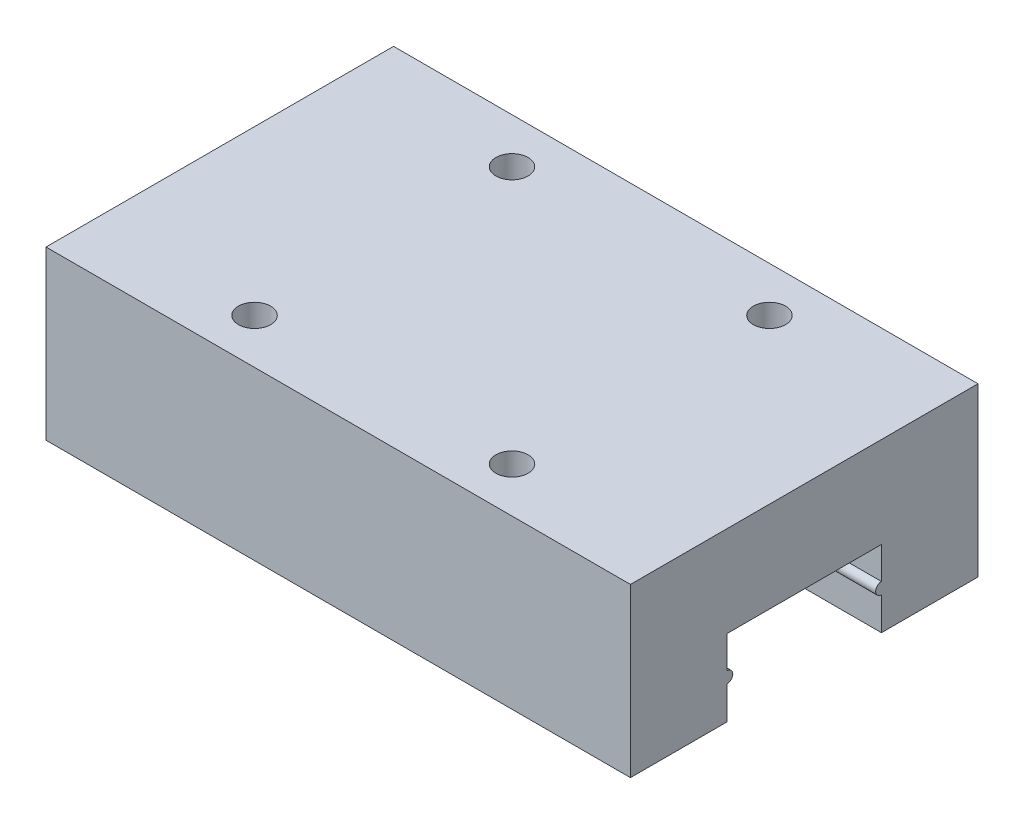
SolidWorks part; units mm, degrees
ref_plane "Front Plane" through (0, 0, 0) normal (0, 0, 1) x (1, 0, 0)
ref_plane "Top Plane" through (0, 0, 0) normal (0, 1, 0) x (1, 0, 0)
ref_plane "Right Plane" through (0, 0, 0) normal (1, 0, 0) x (0, 0, -1)
sketch "Sketch1" plane through (0, 0, 0) normal (1, 0, 0) x (0, 0, -1)
  line L0 (7.5, 0) -> (7.5, 5.9415)
  line L5 (7.5, 0) -> (19.5, 0)
  line L6 (0, 0) -> (0, 13)
  line L7 (0, 13) -> (27, 13)
  line L8 (27, 0) -> (27, 13)
  line L13 (7.5, 5.9415) -> (19.5, 5.9415)
  line L14 (19.5, 5.9415) -> (19.5, 0)
  line L15 (0, 0) -> (7.5, 0)
  line L16 (19.5, 0) -> (27, 0)
  line L17 (13.5, 5.9415) -> (13.5, 0) construction
  arc A0 (7.5, 3.45) -> (7.5, 2.55) centre (7.5, 3) cw
  arc A1 (19.5, 3.45) -> (19.5, 2.55) centre (19.5, 3) ccw
  point P4 (13.5, 0)
  point P12 (7.5, 3)
  dimension "D6" = 0.45
  dimension "D1" = 13
  dimension "D2" = 27
  dimension "D3" = 7.0585
  dimension "D4" = 12
  dimension "D5" = 3
extrude "Boss-Extrude1" add sketch "Sketch1" along normal blind 45.4 contours L14 L16 L8 L7 L6 L15 L0 L13 | A0 L0 | L14 A1
hole_wizard "M3x0.5 Tapped Hole1" positions "Sketch2" profile "Sketch3" tap size "M3x0.5" standard "JIS"
sketch "Sketch2" plane through (0, 13, 0) normal (0, 1, 0) x (1, 0, 0)
  line L1 (45.4, 27) -> (0, 27) construction
  line L2 (0, 0) -> (0, 27) construction
  point P0 (12.7, 23.5)
  dimension "D1" = 3.5
  dimension "D2" = 12.7
sketch "Sketch3" plane through (12.7, 13, -23.5) normal (1, 0, 0) x (0, 0, 1)
  line L0 (0, 0) -> (0, 4.2511)
  line L1 (0, 4.2511) -> (1.25, 3.5)
  line L2 (1.25, 3.5) -> (1.25, 0)
  line L5 (1.25, 0) -> (0, 0)
  line L10 (0, 4.2511) -> (-1.25, 3.5) construction
  line L11 (0, -6.35) -> (0, 107.95) construction
  dimension "Tap Drill Dia." = 2.5
  dimension "Tap Drill Depth" = 3.5
  dimension "Drill Angle" = 118
cosmetic thread "Hole Thread1" parameters "D1"=6, "D2"=3
pattern_linear "LPattern1" count 2 spacing 20 along (1, 0, 0) count 2 spacing 20 along (0, 0, 1) of "M3x0.5 Tapped Hole1"
cosmetic thread "Hole Thread2" parameters "D1"=6, "D2"=3
cosmetic thread "Hole Thread3" parameters "D1"=6, "D2"=3
cosmetic thread "Hole Thread4" parameters "D1"=6, "D2"=3
